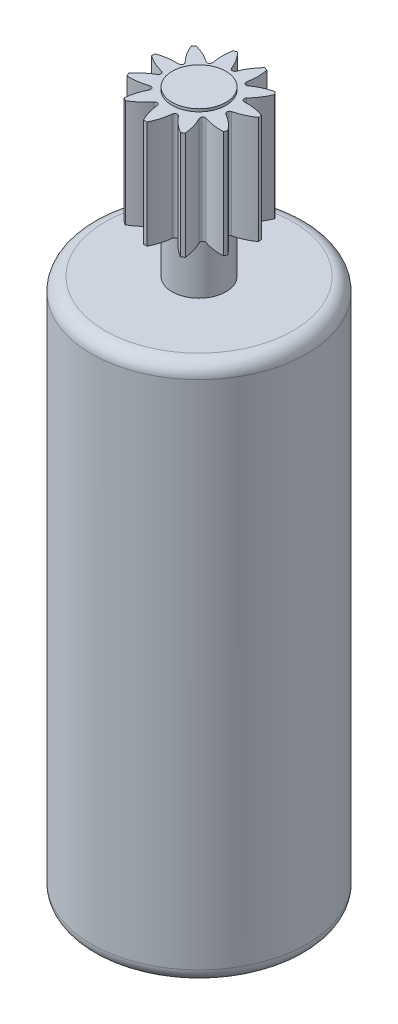
SolidWorks part; units mm, degrees
ref_plane "Front Plane" through (0, 0, 0) normal (0, 0, 1) x (1, 0, 0)
ref_plane "Top Plane" through (0, 0, 0) normal (0, 1, 0) x (1, 0, 0)
ref_plane "Right Plane" through (0, 0, 0) normal (1, 0, 0) x (0, 0, -1)
sketch "Sketch3" plane through (0, 0, 0) normal (0, 0, 1) x (1, 0, 0)
  line L0 (0, 0) -> (0, 26.1)
  line L1 (0, 0) -> (4, 0)
  line L2 (4, 0) -> (4, 20)
  line L3 (4, 20) -> (1, 20)
  line L4 (1, 20) -> (1, 22)
  line L5 (1, 22) -> (2, 22)
  line L6 (2, 22) -> (2, 26)
  line L7 (2, 26) -> (1, 26)
  line L8 (1, 26) -> (1, 26.1)
  line L9 (1, 26.1) -> (0, 26.1)
  dimension "D1" = 26.1
  dimension "D2" = 4
  dimension "D3" = 20
  dimension "D4" = 3
  dimension "D5" = 2
  dimension "D6" = 1
  dimension "D7" = 4
  dimension "D8" = 1
  dimension "D9" = 0.1
revolve "Revolve1" add sketch "Sketch3" angle 360 about L0
fillet "Fillet1" radius 0.5 2 edges at (0, 0, -4) (0, 20, -4)
sketch "Sketch4" plane through (0, 26, 0) normal (0, 1, 0) x (1, 0, 0)
  line L0 (0, 0) -> (0, 2.8828) construction
  arc A0 (-0.5, 1.9365) -> (-0.0929, 1.2999) centre (-1.951, 0.5601) cw
  circle A1 centre (0, 0) radius 2 construction
  circle A2 centre (0, 0) radius 1 construction
  arc A3 (0.0929, 1.2999) -> (0.5, 1.9365) centre (1.951, 0.5601) cw
  arc A4 (0.5, 1.9365) -> (-0.5, 1.9365) centre (0, 0) ccw
  arc A5 (-0.0929, 1.2999) -> (0.0929, 1.2999) centre (0, 1.3369) ccw
  point P14 (0, 1)
  dimension "D1" = 1
  dimension "D2" = 2
  dimension "D3" = 2
  dimension "D4" = 0.1
extrude "Cut-Extrude1" cut sketch "Sketch4" against normal blind 4
pattern_circular "CirPattern1" count 11 over 360 about axis through (0, 0, 0) along (0, 1, 0) of "Cut-Extrude1"
